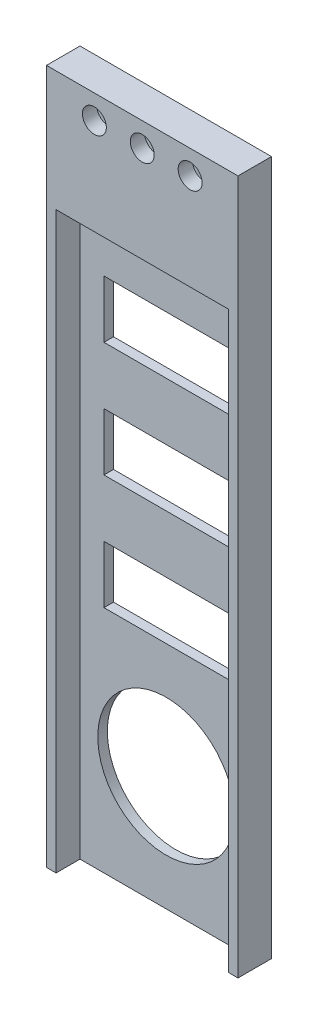
SolidWorks part; units mm, degrees
ref_plane "Front Plane" through (0, 0, 0) normal (0, 0, 1) x (1, 0, 0)
ref_plane "Top Plane" through (0, 0, 0) normal (0, 1, 0) x (1, 0, 0)
ref_plane "Right Plane" through (0, 0, 0) normal (1, 0, 0) x (0, 0, -1)
sketch "Sketch1" plane through (0, 0, 0) normal (0, 0, 1) x (1, 0, 0)
  line L1 (0, 0) -> (40, 0)
  line L2 (0, 0) -> (0, 145.1)
  line L3 (0, 145.1) -> (40, 145.1)
  line L4 (40, 0) -> (40, 145.1)
  dimension "D1" = 40
  dimension "D2" = 145.1
extrude "Boss-Extrude1" add sketch "Sketch1" along normal blind 2
sketch "Sketch2" plane through (0, 0, 2) normal (0, 0, 1) x (1, 0, 0)
  line L0 (40, 0) -> (40, 145.1) construction
  line L1 (40, 145.1) -> (0, 145.1) construction
  circle A0 centre (20, 24) radius 14.29
  dimension "D1" = 28.58
  dimension "D2" = 20
  dimension "D3" = 121.1
extrude "Cut-Extrude1" cut sketch "Sketch2" against normal blind 2
sketch "Sketch3" plane through (0, 0, 2) normal (0, 0, 1) x (1, 0, 0)
  line L0 (0, 145.1) -> (40, 145.1)
  line L1 (40, 145.1) -> (0, 145.1) construction
  line L2 (40, 145.1) -> (40, 0)
  line L3 (40, 0) -> (40, 145.1) construction
  line L4 (40, 0) -> (38, 0)
  line L5 (0, 0) -> (40, 0) construction
  line L6 (38, 0) -> (38, 120)
  line L7 (38, 120) -> (2, 120)
  line L8 (2, 120) -> (2, 0)
  line L9 (2, 0) -> (0, 0)
  line L10 (0, 0) -> (0, 145.1)
  dimension "D1" = 2
  dimension "D2" = 2
  dimension "D3" = 120
extrude "Boss-Extrude2" add sketch "Sketch3" along normal blind 5
sketch "Sketch4" plane through (0, 0, 7) normal (0, 0, 1) x (1, 0, 0)
  line L0 (40, 145.1) -> (0, 145.1) construction
  line L1 (0, 145.1) -> (0, 0) construction
  line L2 (40, 0) -> (40, 145.1) construction
  circle A0 centre (20, 140.1) radius 1.25
  circle A1 centre (10, 140.1) radius 1.25
  circle A2 centre (30, 140.1) radius 1.25
  dimension "D1" = 2.5
  dimension "D2" = 5
  dimension "D3" = 2.5
  dimension "D4" = 2.5
  dimension "D5" = 10
  dimension "D6" = 10
extrude "Cut-Extrude2" cut sketch "Sketch4" against normal blind 7
sketch "Sketch5" plane through (0, 0, 7) normal (0, 0, 1) x (1, 0, 0)
  circle A0 centre (10, 140.1) radius 2.5
  circle A1 centre (20, 140.1) radius 2.5
  circle A2 centre (30, 140.1) radius 2.5
  dimension "D1" = 5
  dimension "D2" = 5
  dimension "D3" = 5
extrude "Cut-Extrude3" cut sketch "Sketch5" against normal blind 3
sketch "Sketch6" plane through (0, 0, 2) normal (0, 0, 1) x (1, 0, 0)
  line L0 (2, 0) -> (2, 120) construction
  line L1 (7, 108) -> (33, 108)
  line L2 (7, 108) -> (7, 96)
  line L3 (7, 96) -> (33, 96)
  line L4 (33, 108) -> (33, 96)
  line L5 (7, 84) -> (33, 84)
  line L6 (7, 84) -> (7, 72)
  line L7 (7, 72) -> (33, 72)
  line L8 (33, 84) -> (33, 72)
  line L9 (7, 48) -> (33, 48)
  line L10 (7, 48) -> (7, 60)
  line L11 (7, 60) -> (33, 60)
  line L12 (33, 48) -> (33, 60)
  line L13 (38, 120) -> (38, 0) construction
  line L14 (2, 0) -> (2, 120) construction
  line L15 (38, 120) -> (38, 0) construction
  line L16 (2, 120) -> (38, 120) construction
  dimension "D1" = 5
  dimension "D2" = 5
  dimension "D3" = 5
  dimension "D4" = 5
  dimension "D5" = 5
  dimension "D6" = 5
  dimension "D7" = 12
  dimension "D8" = 12
  dimension "D9" = 12
  dimension "D10" = 12
  dimension "D11" = 12
  dimension "D12" = 12
extrude "Cut-Extrude4" cut sketch "Sketch6" against normal through all
